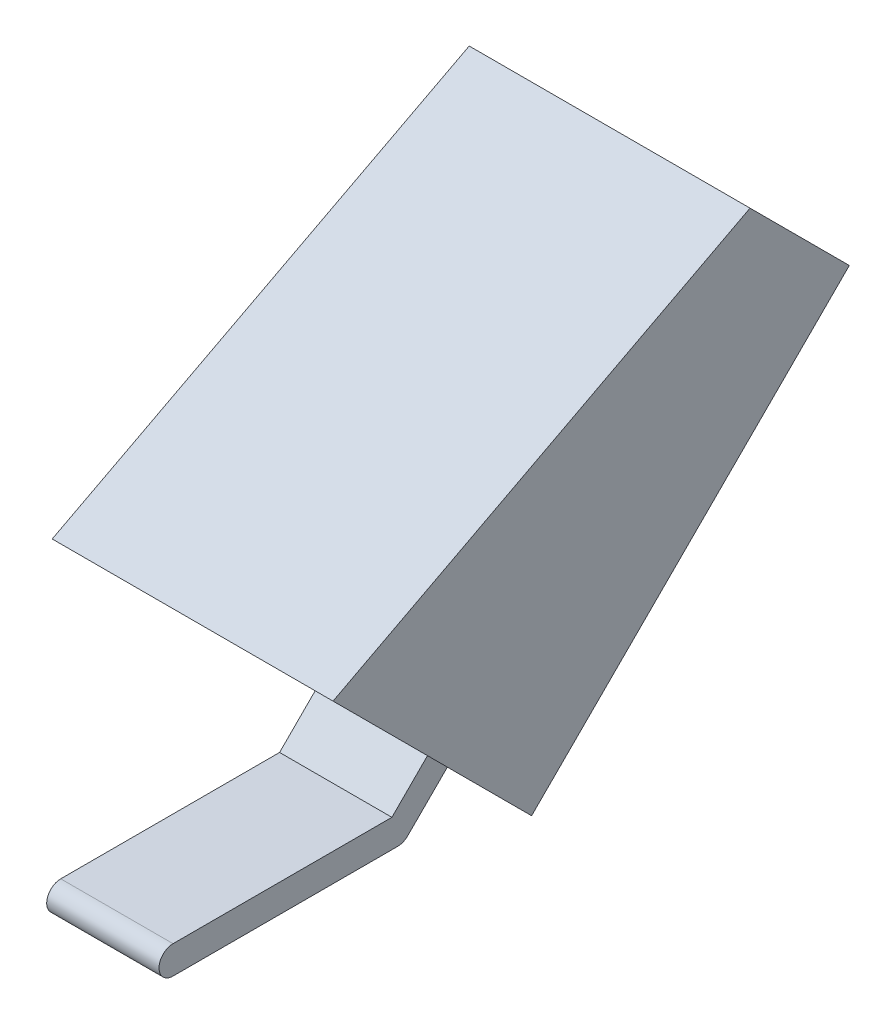
SolidWorks part; units mm, degrees
ref_plane "Front" through (0, 0, 0) normal (0, 0, 1) x (1, 0, 0)
ref_plane "Top" through (0, 0, 0) normal (0, 1, 0) x (1, 0, 0)
ref_plane "Right" through (0, 0, 0) normal (1, 0, 0) x (0, 0, -1)
sketch "草图1" plane through (0, 0, 0) normal (1, 0, 0) x (0, 0, -1)
  line L0 (-8, 0) -> (8, 0) construction
  line L1 (-8, 1) -> (7.5858, 1)
  line L2 (-8, -1) -> (8, -1)
  line L3 (8, 0) -> (24.1742, 16.1742) construction
  line L4 (8, 0) -> (27.799, 19.799) construction
  line L5 (7.5858, 1) -> (27.0919, 20.5061)
  line L6 (8.7071, -0.7071) -> (28.5061, 19.0919)
  arc A0 (-8, 1) -> (-8, -1) centre (-8, 0) ccw
  arc A1 (8, -1) -> (8.7071, -0.7071) centre (8, 0) ccw
  arc A2 (8, -1) -> (8.7071, -0.7071) centre (8, 0) ccw
  arc A3 (28.5061, 19.0919) -> (27.0919, 20.5061) centre (27.799, 19.799) ccw
  point P2 (0, 0)
  point P11 (17.8995, 9.8995)
  dimension "D1" = 135
extrude "凸台-拉伸2" add sketch "草图1" along normal mid plane 8 contours L6 A3 L5 L1 A1 | A2 L5 L1 A0 L2
sketch "草图5" plane through (0, -4.7071, -4.7071) normal (0, -0.7071, -0.7071) x (1, 0, 0)
  line L0 (0, -5.6569) -> (0, -36.6143) construction
  line L1 (4, -5.6569) -> (-4, -5.6569) construction
  line L3 (-10, -9.6569) -> (10, -9.6569)
  line L4 (-10, -9.6569) -> (-10, -41.6569)
  line L5 (-10, -41.6569) -> (10, -41.6569)
  line L6 (10, -9.6569) -> (10, -41.6569)
  dimension "D1" = 4
  dimension "D2" = 32
  dimension "D3" = 20
  dimension "D4" = 10
extrude "凸台-拉伸5" add sketch "草图5" against normal blind 20
sketch "草图6" plane through (-10, 0, 0) normal (-1, 0, 0) x (0, 0, 1)
  line L0 (2.6066, 16.2635) -> (-27.0919, 31.8198)
  line L1 (-20.0208, 38.8909) -> (-34.163, 24.7487) construction
  line L2 (-27.0919, 31.8198) -> (-20.0208, 38.8909)
  line L3 (-20.0208, 38.8909) -> (2.6066, 16.2635)
extrude "切除-拉伸3" cut sketch "草图6" against normal blind 20
